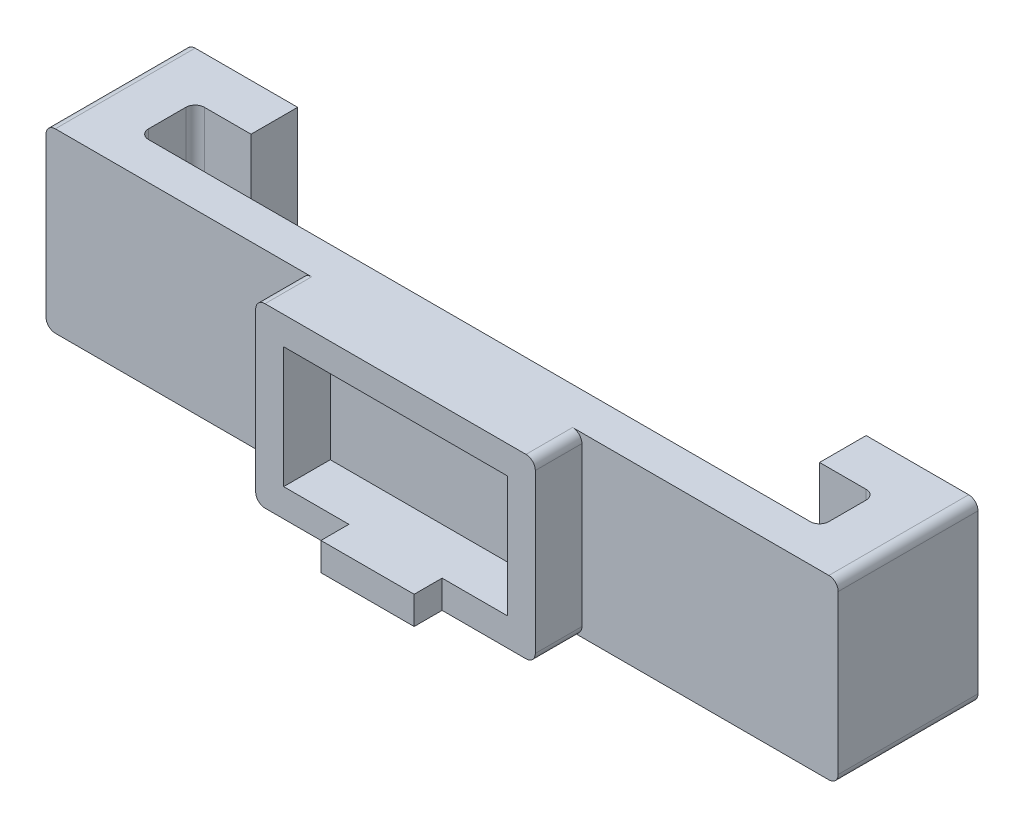
SolidWorks part; units mm, degrees
ref_plane "Front Plane" through (0, 0, 0) normal (0, 0, 1) x (1, 0, 0)
ref_plane "Top Plane" through (0, 0, 0) normal (0, 1, 0) x (1, 0, 0)
ref_plane "Right Plane" through (0, 0, 0) normal (1, 0, 0) x (0, 0, -1)
sketch "Sketch1" plane through (0, 0, 0) normal (0, 0, 1) x (1, 0, 0)
  line L1 (0, 0) -> (24, 0)
  line L2 (0, 0) -> (0, 13)
  line L3 (0, 13) -> (24, 13)
  line L4 (24, 0) -> (24, 13)
  line L5 (-3, 16) -> (27, 16)
  line L6 (-3, 16) -> (-3, -3)
  line L7 (-3, -3) -> (27, -3)
  line L8 (27, 16) -> (27, -3)
  point P9 (0, 0)
  point P10 (0, 0)
  point P11 (0, 0)
  point P12 (0, 0)
  point P13 (0, 0)
  point P14 (0, 0)
  point P15 (0, 0)
  point P16 (0, 0)
  point P17 (0, 0)
  point P18 (0, 0)
  point P19 (0, 0)
  point P20 (0, 0)
  point P21 (0, 0)
  point P22 (0, 0)
  point P23 (0, 0)
  point P24 (0, 0)
  point P25 (0, 0)
  point P26 (0, 0)
extrude "Boss-Extrude1" add sketch "Sketch1" along normal blind 5
sketch "Sketch3" plane through (0, 0, 0) normal (0, 0, -1) x (-1, 0, 0)
  line L7 (-27, 16) -> (3, 16) construction
  line L9 (-12, 16) -> (-54.5, 16)
  line L11 (-7, -3) -> (-54.5, -3)
  line L12 (-54.5, 16) -> (-54.5, -3)
  line L13 (-12, 16) -> (30.5, 16)
  line L15 (-7, -3) -> (30.5, -3)
  line L16 (30.5, 16) -> (30.5, -3)
  point P4 (0, 0)
extrude "Boss-Extrude4" add sketch "Sketch3" along normal blind 4 contours L13 L16 L15 L11 L12 L9
sketch "Sketch4" plane through (0, 0, -4) normal (0, 0, -1) x (-1, 0, 0)
  line L0 (30.5, -3) -> (-54.5, -3) construction
  line L1 (-54.5, 16) -> (-48.5, 16)
  line L2 (-54.5, 16) -> (-54.5, -3)
  line L3 (-54.5, -3) -> (-48.5, -3)
  line L4 (-48.5, 16) -> (-48.5, -3)
  point P7 (0, 0)
  point P8 (0, 0)
extrude "Boss-Extrude5" add sketch "Sketch4" along normal blind 6
pattern_linear "LPattern1" count 2 spacing 79 along (-1, 0, 0) of "Boss-Extrude5"
sketch "Sketch6" plane through (0, 0, -10) normal (0, 0, -1) x (-1, 0, 0)
  line L0 (24.5, -3) -> (-48.5, -3) construction
  line L1 (-54.5, 16) -> (-42.5, 16)
  line L2 (-54.5, 16) -> (-54.5, -3)
  line L3 (-54.5, -3) -> (-42.5, -3)
  line L4 (-42.5, 16) -> (-42.5, -3)
extrude "Boss-Extrude6" add sketch "Sketch6" along normal blind 5
pattern_linear "LPattern2" count 2 spacing 73 along (-1, 0, 0) of "Boss-Extrude6"
sketch "Sketch7" plane through (0, 0, 5) normal (0, 0, 1) x (1, 0, 0)
  line L7 (0, 0) -> (24, 0) construction
  line L8 (-3, -3) -> (27, -3) construction
  line L10 (12, 0) -> (7, 0)
  line L12 (12, -3) -> (7, -3)
  line L13 (7, 0) -> (7, -3)
  line L14 (12, 0) -> (17, 0)
  line L16 (12, -3) -> (17, -3)
  line L17 (17, 0) -> (17, -3)
extrude "Boss-Extrude7" add sketch "Sketch7" along normal blind 3
fillet "Fillet1" radius 1 4 edges at (27, 16, 2.5) (27, -3, 2.5) (-3, -3, 2.5) (-3, 16, 2.5)
fillet "Fillet2" radius 1 4 edges at (54.5, 16, -7.5) (54.5, -3, -7.5) (-30.5, -3, -7.5) (-30.5, 16, -7.5)
fillet "Fillet3" radius 1 4 edges at (-24.5, 6.5, -4) (48.5, 6.5, -4) (48.5, 6.5, -10) (-24.5, 6.5, -10)
